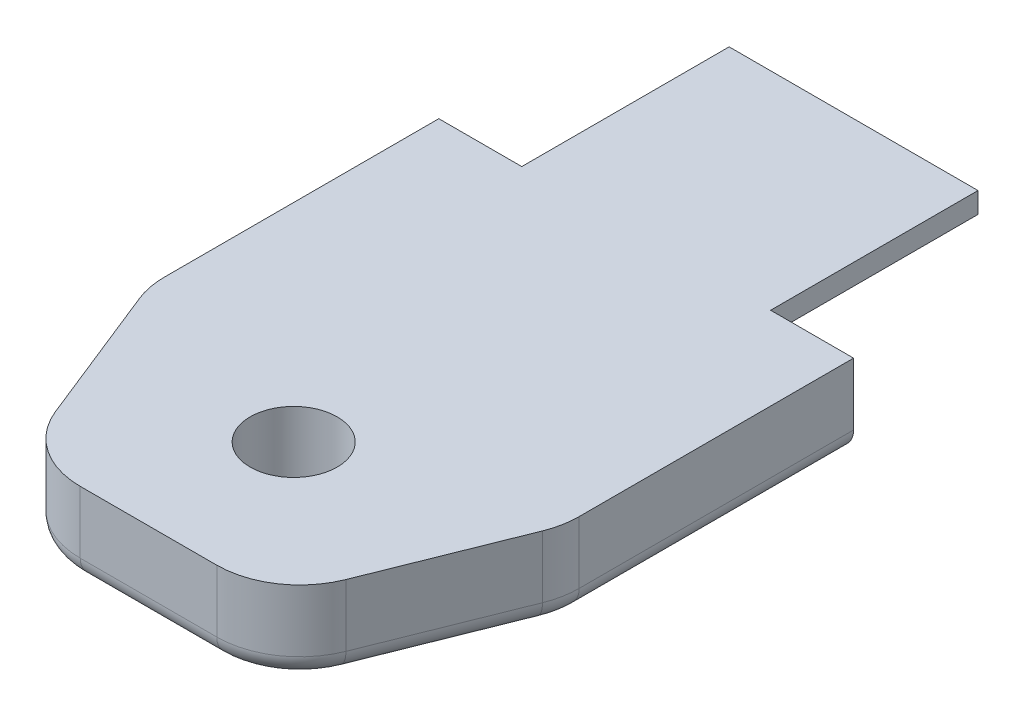
SolidWorks part; units mm, degrees
ref_plane "Plan de face" through (0, 0, 0) normal (0, 0, 1) x (1, 0, 0)
ref_plane "Plan de dessus" through (0, 0, 0) normal (0, 1, 0) x (1, 0, 0)
ref_plane "Plan de droite" through (0, 0, 0) normal (1, 0, 0) x (0, 0, -1)
sketch "Esquisse1" plane through (0, 0, 0) normal (0, 0, 1) x (1, 0, 0)
  line L0 (-3, 0) -> (3, 0)
  line L1 (3, 0) -> (6, 3)
  line L2 (6, 3) -> (6, 4)
  line L3 (6, 4) -> (-6, 4)
  line L4 (-6, 4) -> (-6, 3)
  line L5 (-6, 3) -> (-3, 0)
  dimension "D1" = 3
  dimension "D2" = 3
  dimension "D3" = 3
  dimension "D4" = 3
  dimension "D5" = 6
  dimension "D6" = 12
  dimension "D7" = 4
extrude "Boss.-Extru.1" add sketch "Esquisse1" along normal blind 10
sketch "Esquisse2" plane through (0, 0, 10) normal (0, 0, 1) x (1, 0, 0)
  line L0 (-3, 0) -> (3, 0) construction
  line L1 (-10, 0) -> (10, 0)
  line L2 (-10, 0) -> (-10, 4)
  line L3 (-10, 4) -> (10, 4)
  line L4 (10, 0) -> (10, 4)
  dimension "D1" = 20
  dimension "D2" = 10
  dimension "D3" = 4
extrude "Boss.-Extru.2" add sketch "Esquisse2" along normal blind 24
sketch "Esquisse3" plane through (0, 0, 0) normal (0, -1, 0) x (1, 0, 0)
  line L0 (0, 0) -> (0, 34) construction
  line L1 (-10, 34) -> (10, 34) construction
  circle A1 centre (0, 27) radius 2.1
  dimension "D2" = 4.2
  dimension "D3" = 7
extrude "Enlèv. mat.-Extru.1" cut sketch "Esquisse3" against normal through all
chamfer "Chanfrein1" distance 10 distance2 4 2 edges at (10, 2, 34) (-10, 2, 34)
fillet "Congé1" radius 4 4 edges at (-10, 2, 24) (-6, 2, 34) (10, 2, 24) (6, 2, 34)
fillet "Congé2" radius 1 9 edges at (10, 0, 16.6148) (9.9278, 0, 23.9861) (8.3598, 0, 28.1004) (5.5344, 0, 33.3123) (0, 0, 34) (-5.5344, 0, 33.3123) (-8.3598, 0, 28.1004) (-9.9278, 0, 23.9861) (-10, 0, 16.6148)
